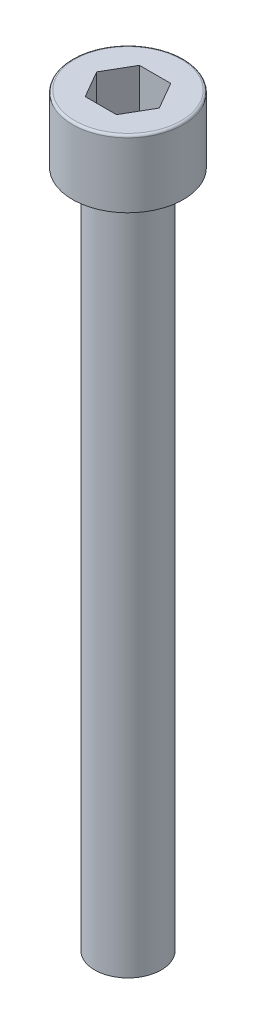
SolidWorks part; units mm, degrees
ref_plane "Alzado" through (0, 0, 0) normal (0, 0, 1) x (1, 0, 0)
ref_plane "Planta" through (0, 0, 0) normal (0, 1, 0) x (1, 0, 0)
ref_plane "Vista lateral" through (0, 0, 0) normal (1, 0, 0) x (0, 0, -1)
sketch "Croquis1" plane through (0, 0, 0) normal (0, 0, 1) x (1, 0, 0)
  line L0 (0, 37.7354) -> (0, -28.2646)
  line L1 (0, -28.2646) -> (-2, -28.2646)
  line L2 (-2, -28.2646) -> (-2.925, -27.7646)
  line L3 (-2.925, -27.7646) -> (-2.925, 31.8354)
  line L4 (-2.925, 31.8354) -> (-4.875, 31.8354)
  line L5 (-4.875, 31.8354) -> (-4.875, 37.7354)
  line L6 (-4.875, 37.7354) -> (0, 37.7354)
  dimension "D1" = 66
  dimension "D2" = 4.875
  dimension "D3" = 2.925
  dimension "D4" = 5.9
  dimension "D5" = 0.5
  dimension "D6" = 2
revolve "Revolución1" add sketch "Croquis1" angle 360 about L0
sketch "Croquis2" plane through (0, 37.7354, 0) normal (0, 1, 0) x (1, 0, 0)
  line L1 (2.75, 0) -> (1.375, 2.3816)
  line L2 (1.375, 2.3816) -> (-1.375, 2.3816)
  line L3 (-1.375, 2.3816) -> (-2.75, 0)
  line L4 (-2.75, 0) -> (-1.375, -2.3816)
  line L5 (-1.375, -2.3816) -> (1.375, -2.3816)
  line L6 (1.375, -2.3816) -> (2.75, 0)
  circle A0 centre (0, 0) radius 2.3816 construction
  dimension "D1" = 5.5
extrude "Cortar-Extruir1" cut sketch "Croquis2" against normal blind 3.9
fillet "Redondeo1" radius 0.2 1 edges at (-4.875, 37.7354, 0)
